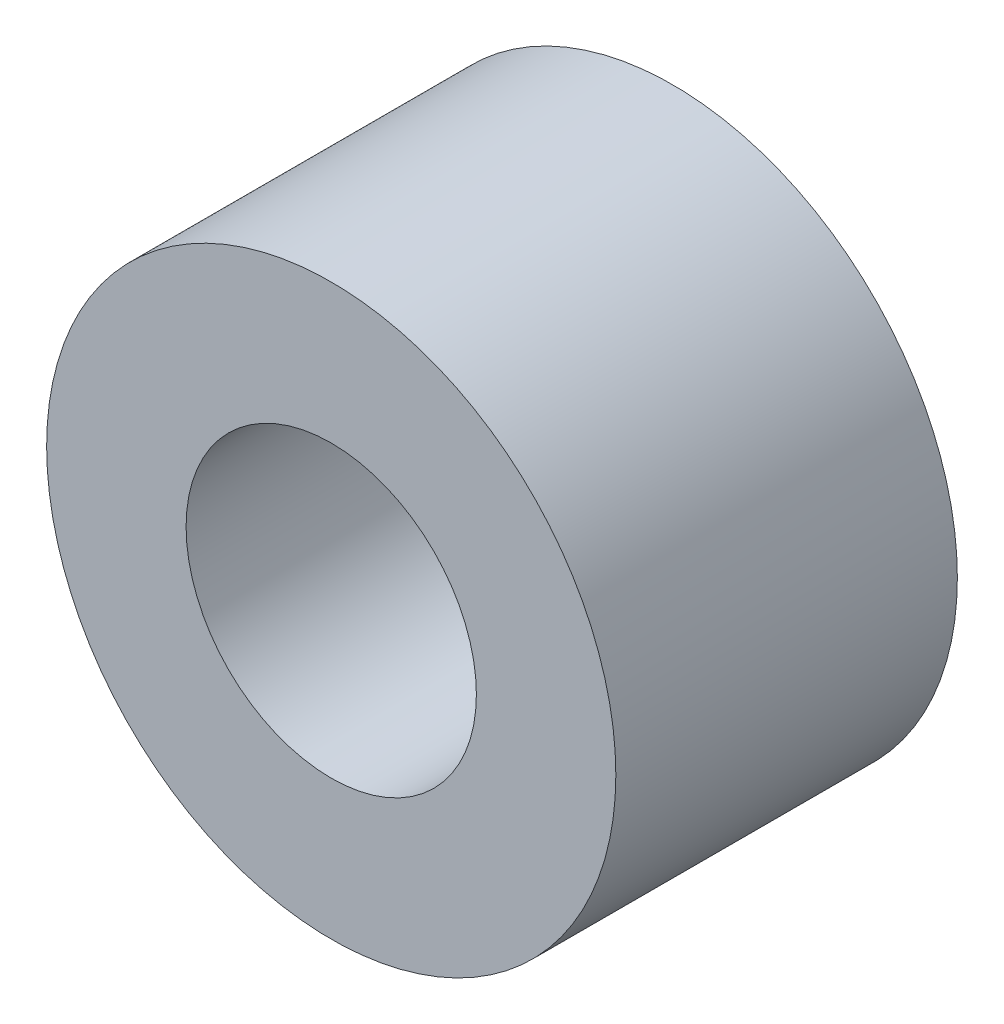
SolidWorks part; units mm, degrees
material "6063-T6"
ref_plane "Front Plane" through (0, 0, 0) normal (0, 0, 1) x (1, 0, 0)
ref_plane "Top Plane" through (0, 0, 0) normal (0, 1, 0) x (1, 0, 0)
ref_plane "Right Plane" through (0, 0, 0) normal (1, 0, 0) x (0, 0, -1)
sketch "Sketch2" plane through (0, 0, 0) normal (0, 0, 1) x (1, 0, 0)
  circle A0 centre (0, 0) radius 2.55
  circle A1 centre (0, 0) radius 5
  dimension "D1" = 5.1
  dimension "D2" = 10
extrude "Boss-Extrude1" add sketch "Sketch2" along normal blind 6
